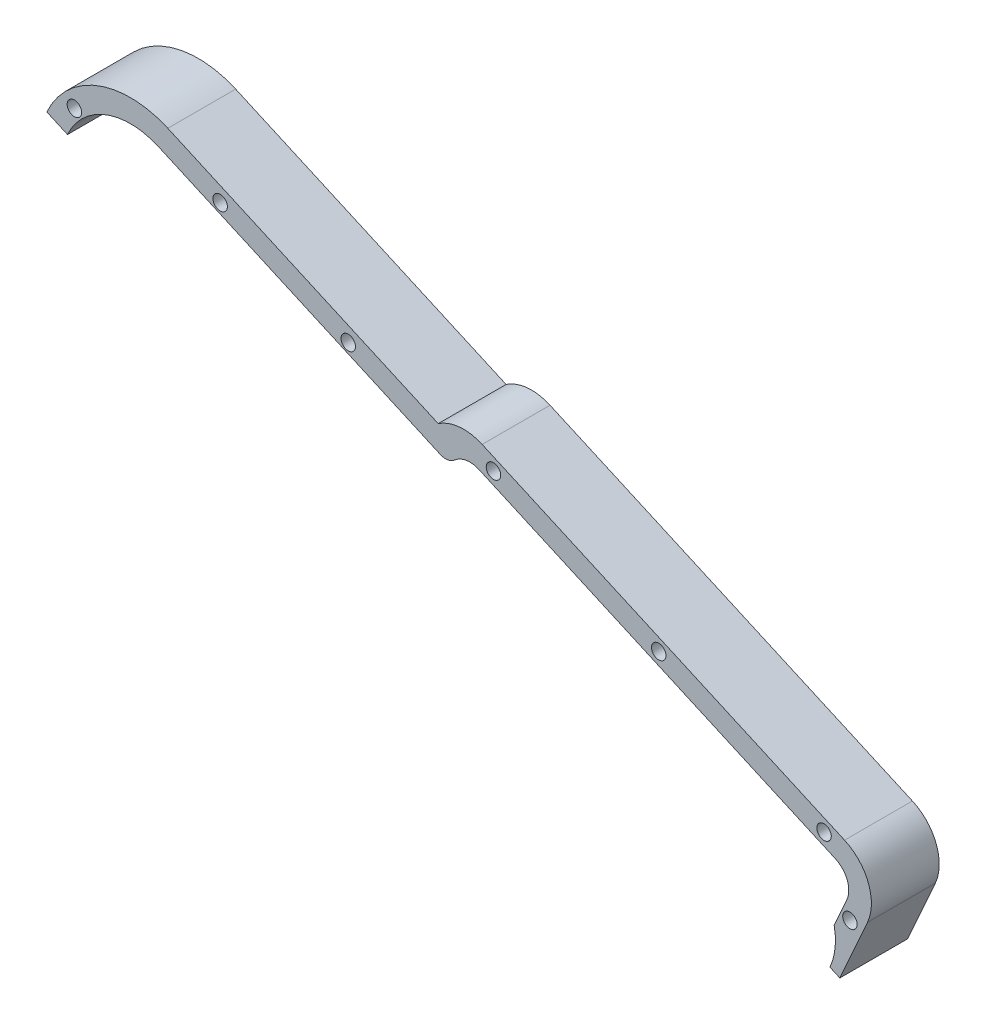
SolidWorks part; units mm, degrees
ref_plane "Front Plane" through (0, 0, 0) normal (0, 0, 1) x (1, 0, 0)
ref_plane "Top Plane" through (0, 0, 0) normal (0, 1, 0) x (1, 0, 0)
ref_plane "Right Plane" through (0, 0, 0) normal (1, 0, 0) x (0, 0, -1)
sketch "Sketch1" plane through (0, 0, 0) normal (0, 0, 1) x (1, 0, 0)
  line L0 (-81.4496, 53.8056) -> (-67.7738, 84.4844) construction
  line L1 (-91.6421, 47.2686) -> (-171.5223, 82.8771) construction
  line L2 (-75.2645, 89.2365) -> (-149.4221, 122.2941) construction
  line L3 (-72.7153, 90.8373) -> (-152.817, 126.5446)
  line L5 (-173.1746, 80.8766) -> (-93.0729, 45.1693)
  line L6 (-79.8678, 50.2314) -> (-67.6532, 77.6322)
  line L7 (-176.5357, 89.3012) -> (-161.0339, 124.0762) construction
  line L8 (-168.9326, 106.3571) -> (-73.7605, 63.9318) construction
  line L9 (-133.1238, 63.0229) -> (-112.7662, 108.691) construction
  line L10 (-162.5246, 125.6714) -> (-222.2994, 152.3174)
  line L11 (-73.7605, 63.9318) -> (-275.2251, 153.7395) construction
  line L12 (-179.0143, 88.6803) -> (-238.789, 115.3263)
  circle A0 centre (-230.5442, 133.8219) radius 14.25
  circle A2 centre (-95.5715, 49.0202) radius 1.7
  arc A3 (-152.817, 126.5446) -> (-162.5246, 125.6714) centre (-156.8885, 117.411) ccw
  arc A4 (-179.0143, 88.6803) -> (-173.1746, 80.8766) centre (-169.1031, 90.0102) ccw
  arc A5 (-93.0729, 45.1693) -> (-79.8678, 50.2314) centre (-89.0014, 54.3029) ccw
  arc A6 (-67.6532, 77.6322) -> (-72.7153, 90.8373) centre (-76.7868, 81.7037) ccw
  circle A7 centre (-132.1059, 65.3063) radius 1.7
  circle A8 centre (-168.6403, 81.5924) radius 1.7
  circle A9 centre (-150.3184, 122.6936) radius 1.6
  circle A10 centre (-113.784, 106.4076) radius 1.6
  circle A11 centre (-77.2496, 90.1215) radius 1.6
  circle A13 centre (-81.2951, 54.1522) radius 1.7
  circle A14 centre (-71.5234, 76.0729) radius 1.6
  circle A17 centre (-168.9326, 106.3571) radius 1.7
  arc A18 (-222.2994, 152.3174) -> (-238.789, 115.3263) centre (-230.5442, 133.8219) ccw
  dimension "D4" = 12
  dimension "D6" = 3.2
  dimension "D7" = 3.2
  dimension "D8" = 3.2
  dimension "D9" = 3.4
  dimension "D10" = 3.4
  dimension "D11" = 3.4
  dimension "D12" = 3.4
  dimension "D13" = 3.2
  dimension "D14" = 3.4
  dimension "D23" = 28.5
  dimension "D25" = 6
  dimension "D3" = 12
  dimension "D5" = 171.6559
  dimension "D1" = 2.5
  dimension "D2" = 2.5
  dimension "D15" = 0
  dimension "D16" = 0
  dimension "D17" = 40
  dimension "D18" = 40
  dimension "D20" = 40
  dimension "D21" = 40
extrude "Boss-Extrude1" add sketch "Sketch1" along normal blind 15
sketch "Sketch5" plane through (0, 0, 15) normal (0, 0, 1) x (1, 0, 0)
  line L0 (-181.3663, 93.0133) -> (-237.5676, 118.0664) construction
  line L1 (-238.789, 115.3263) -> (-179.0143, 88.6803) construction
  line L2 (-165.0202, 123.4993) -> (-223.5208, 149.5773) construction
  line L3 (-162.5246, 125.6714) -> (-222.2994, 152.3174) construction
  line L4 (-168.9326, 106.3571) -> (-249.0397, 142.0667) construction
  line L5 (-230.5442, 133.8219) -> (-247.7516, 135.033) construction
  line L6 (-242.9474, 145.8104) -> (-230.5442, 133.8219) construction
  line L7 (-196.4664, 99.7446) -> (-182.4196, 131.2555) construction
  line L8 (-224.7805, 112.3663) -> (-210.7338, 143.8772) construction
  circle A0 centre (-230.5442, 133.8219) radius 17.25 construction
  arc A1 (-222.2994, 152.3174) -> (-238.789, 115.3263) centre (-230.5442, 133.8219) ccw construction
  circle A2 centre (-196.4664, 99.7446) radius 1.25
  circle A3 centre (-224.7805, 112.3663) radius 1.25
  circle A4 centre (-210.7338, 143.8772) radius 1.6
  circle A5 centre (-182.4196, 131.2555) radius 1.6
  circle A6 centre (-242.9474, 145.8104) radius 1.6
  circle A7 centre (-247.7516, 135.033) radius 1.25
  circle A8 centre (-230.5442, 133.8219) radius 14.25 construction
  dimension "D1" = 3
  dimension "D4" = 2.5
  dimension "D5" = 3.2
  dimension "D6" = 3.2
  dimension "D7" = 2.5
  dimension "D8" = 20
  dimension "D9" = 3.2
  dimension "D10" = 20
  dimension "D11" = 2.5
  dimension "D12" = 14
  dimension "D2" = 3
  dimension "D3" = 3
  dimension "D13" = 45
extrude "Cut-Extrude4" cut sketch "Sketch5" against normal through all
sketch "Sketch6" plane through (0, 0, 15) normal (0, 0, 1) x (1, 0, 0)
  line L0 (-158.0596, 123.4073) -> (-70.1843, 84.2348)
  line L1 (-70.1843, 84.2348) -> (-86.4703, 47.7004)
  line L2 (-86.4703, 47.7004) -> (-174.3457, 86.8729)
  line L3 (-174.3457, 86.8729) -> (-158.0596, 123.4073)
  line L4 (-72.7153, 90.8373) -> (-152.817, 126.5446) construction
  line L5 (-173.1746, 80.8766) -> (-93.0729, 45.1693) construction
  line L6 (-79.8678, 50.2314) -> (-67.6532, 77.6322) construction
  dimension "D1" = 5
  dimension "D2" = 5
  dimension "D3" = 5
  dimension "D4" = 5
extrude "Cut-Extrude5" cut sketch "Sketch6" against normal through all
fillet "Fillet1" radius 5 2 edges at (-174.3457, 86.8729, 7.5) (-158.0596, 123.4073, 7.5)
fillet "Fillet2" radius 5 2 edges at (-86.4703, 47.7004, 7.5) (-70.1843, 84.2348, 7.5)
sketch "Sketch7" plane through (0, 0, 15) normal (0, 0, 1) x (1, 0, 0)
  line L0 (-249.0397, 142.0667) -> (-73.7605, 63.9318)
  line L1 (-79.8678, 50.2314) -> (-67.6532, 77.6322) construction
  line L2 (-73.7605, 63.9318) -> (-92.8713, 21.0607)
  line L3 (-92.8713, 21.0607) -> (-268.1506, 99.1956)
  line L4 (-268.1506, 99.1956) -> (-249.0397, 142.0667)
  arc A0 (-222.2994, 152.3174) -> (-238.789, 115.3263) centre (-230.5442, 133.8219) ccw construction
extrude "Cut-Extrude6" cut sketch "Sketch7" against normal through all
sketch "Sketch8" plane through (0, 0, 15) normal (0, 0, 1) x (1, 0, 0)
  line L0 (-147.7431, 113.6079) -> (-224.3351, 147.7506)
  line L1 (-162.5246, 125.6714) -> (-222.2994, 152.3174) construction
  line L2 (-236.831, 119.9281) -> (-160.325, 85.3098)
  line L3 (-160.325, 85.3098) -> (-147.7431, 113.6079)
  arc A0 (-224.3351, 147.7506) -> (-236.831, 119.9281) centre (-230.5442, 133.8219) ccw
  dimension "D1" = 5
extrude "Cut-Extrude7" cut sketch "Sketch8" against normal through all
fillet "Fillet5" radius 3 1 edges at (-159.9879, 119.0663, 7.5)
sketch "Sketch9" plane through (0, 0, 15) normal (0, 0, 1) x (1, 0, 0)
  line L0 (-73.7605, 63.9318) -> (-103.697, 77.2767) construction
  circle A0 centre (-88.7288, 70.6043) radius 14
  dimension "D1" = 28
extrude "Cut-Extrude8" cut sketch "Sketch9" against normal through all
